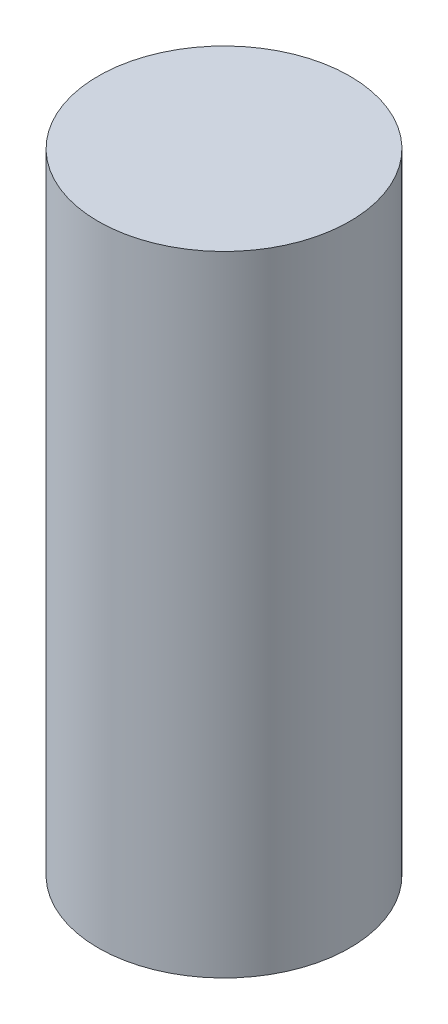
SolidWorks part; units mm, degrees
ref_plane "Front Plane" through (0, 0, 0) normal (0, 0, 1) x (1, 0, 0)
ref_plane "Top Plane" through (0, 0, 0) normal (0, 1, 0) x (1, 0, 0)
ref_plane "Right Plane" through (0, 0, 0) normal (1, 0, 0) x (0, 0, -1)
sketch "Sketch1" plane through (0, 0, 0) normal (0, 1, 0) x (1, 0, 0)
  circle A0 centre (0, 0) radius 25.4
  dimension "D1" = 50.8
extrude "Boss-Extrude1" add sketch "Sketch1" along normal blind 127
hole_wizard "1/4-20 Tapped Hole1" positions "Sketch2" profile "Sketch3" tap size "1/4-20" standard "ANSI Inch"
sketch "Sketch2" plane through (0, 0, 0) normal (0, -1, 0) x (-1, 0, 0)
  line L0 (12.7, 0) -> (-12.7, 0) construction
  point P0 (12.7, 0)
  point P2 (-12.7, 0)
  point P9 (0, 0)
  dimension "D1" = 25.4
sketch "Sketch3" plane through (-12.7, 0, 0) normal (1, 0, 0) x (0, 0, -1)
  line L0 (0, 0) -> (0, 26.9338)
  line L1 (0, 26.9338) -> (2.5527, 25.4)
  line L2 (2.5527, 25.4) -> (2.5527, 0)
  line L5 (2.5527, 0) -> (0, 0)
  line L10 (0, 26.9338) -> (-2.5527, 25.4) construction
  line L11 (0, -6.35) -> (0, 107.95) construction
  dimension "Tap Drill Dia." = 5.1054
  dimension "Tap Drill Depth" = 25.4
  dimension "Drill Angle" = 118
cosmetic thread "Hole Thread1" parameters "D1"=12.7, "D2"=6.35
cosmetic thread "Hole Thread2" parameters "D1"=12.7, "D2"=6.35
